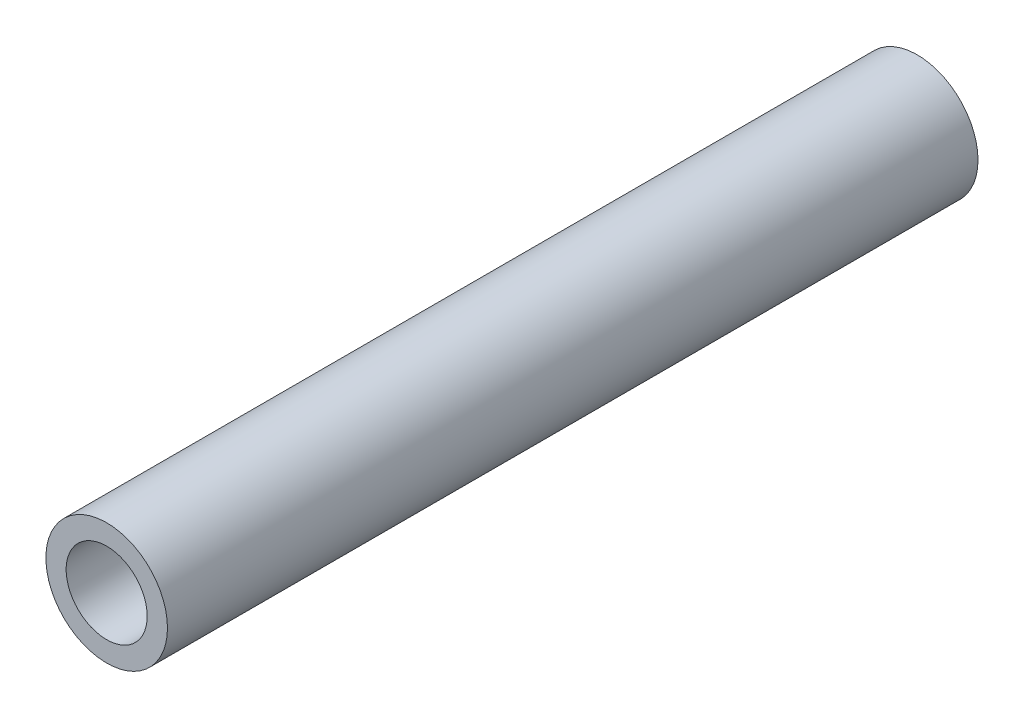
SolidWorks part; units mm, degrees
material "Nylon 101"
ref_plane "Спереди" through (0, 0, 0) normal (0, 0, 1) x (1, 0, 0)
ref_plane "Сверху" through (0, 0, 0) normal (0, 1, 0) x (1, 0, 0)
ref_plane "Справа" through (0, 0, 0) normal (1, 0, 0) x (0, 0, -1)
other "Configuration Table"
sketch "Sketch1" plane through (0, 0, 0) normal (0, 0, 1) x (1, 0, 0)
  circle A0 centre (0, 0) radius 1.5
  circle A1 centre (0, 0) radius 1
extrude "Boss-Extrude1" add sketch "Sketch1" along normal blind 20
